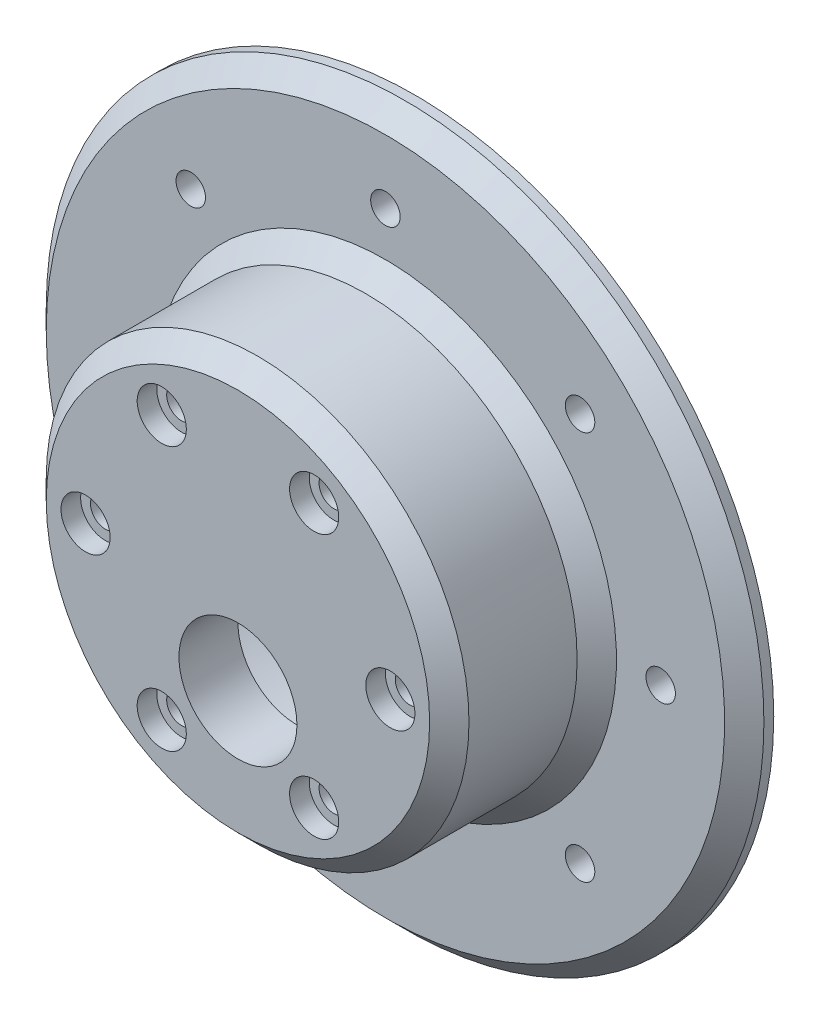
SolidWorks part; units mm, degrees
material "2014 Alloy"
ref_plane "Front Plane" through (0, 0, 0) normal (0, 0, 1) x (1, 0, 0)
ref_plane "Top Plane" through (0, 0, 0) normal (0, 1, 0) x (1, 0, 0)
ref_plane "Right Plane" through (0, 0, 0) normal (1, 0, 0) x (0, 0, -1)
sketch "Sketch1" plane through (0, 0, 0) normal (1, 0, 0) x (0, 0, -1)
  line L0 (0, 0) -> (0, 18.5)
  line L1 (0, 18.5) -> (12, 18.5)
  line L2 (12, 18.5) -> (12, 23.5)
  line L3 (9, 21.5) -> (-6, 21.5)
  line L4 (-6, 21.5) -> (-6, 0)
  line L5 (-6, 0) -> (0, 0)
  line L6 (12, 23.5) -> (11, 23.5)
  line L7 (11, 23.5) -> (11, 25.5)
  line L8 (12, 36.5) -> (9, 36.5)
  line L9 (9, 36.5) -> (9, 21.5)
  line L10 (11, 25.5) -> (12, 25.5)
  line L11 (12, 25.5) -> (12, 36.5)
  dimension "D1" = 18.5
  dimension "D2" = 6
  dimension "D3" = 3
  dimension "D4" = 15
  dimension "D5" = 3
  dimension "D6" = 15
  dimension "D7" = 5
  dimension "D8" = 1
  dimension "D9" = 2
revolve "Revolve1" add sketch "Sketch1" angle 360 about L5
sketch "Sketch2" plane through (0, 0, 6) normal (0, 0, 1) x (1, 0, 0)
  line L0 (0, 0) -> (21.5, 0) construction
  circle A0 centre (0, 0) radius 21.5 construction
hole_wizard "CBORE for M1.6 Hex Head Cap Screw1" positions "Sketch4" profile "Sketch3" counterbore size "M1.6" standard "ISO" end condition through all
sketch "Sketch4" plane through (0, 0, 6) normal (0, 0, 1) x (1, 0, 0)
  point P0 (15.5, 0)
  dimension "D1" = 15.5
sketch "Sketch3" plane through (15.5, 0, 6) normal (1, 0, 0) x (0, -1, 0)
  line L0 (0, 0) -> (0, 18)
  line L1 (0, 18) -> (1.5, 18)
  line L3 (1.5, 18) -> (1.5, 2)
  line L4 (1.5, 2) -> (2.5, 2)
  line L5 (2.5, 2) -> (2.5, 0)
  line L7 (2.5, 0) -> (0, 0)
  line L11 (0, -6.35) -> (0, 107.95) construction
  dimension "Thru Hole Dia." = 3
  dimension "Thru Hole Depth" = 18
  dimension "C'Bore Dia." = 5
  dimension "C'Bore Depth" = 2
pattern_circular "CirPattern1" count 6 over 360 about axis through (0, 0, 0) along (0, 0, 1) of "CBORE for M1.6 Hex Head Cap Screw1"
hole_wizard "Ø12.0mm Dowel Hole1" positions "Sketch6" profile "Sketch5" hole size "Ø12.0" standard "ISO"
sketch "Sketch6" plane through (0, 0, 6) normal (0, 0, 1) x (1, 0, 0)
  point P0 (0, -7)
  dimension "D1" = 7
sketch "Sketch5" plane through (0, -7, 6) normal (1, 0, 0) x (0, -1, 0)
  line L0 (0, 0) -> (0, 18.6052)
  line L1 (0, 18.6052) -> (6, 15)
  line L2 (6, 15) -> (6, 0)
  line L5 (6, 0) -> (0, 0)
  line L10 (0, 18.6052) -> (-6, 15) construction
  line L11 (0, -6.35) -> (0, 107.95) construction
  dimension "Hole Dia." = 12
  dimension "Hole Depth" = 15
  dimension "Drill Angle" = 118
chamfer "Chamfer1" distance 2 angle 45 3 edges at (21.5, 0, 6) (36.5, 0, -9) (21.5, 0, -9)
hole_wizard "Ø3.0mm Dowel Hole3" positions "Sketch8" profile "Sketch7" hole size "Ø3.0" standard "ISO"
sketch "Sketch8" plane through (0, 0, -9) normal (0, 0, 1) x (1, 0, 0)
  circle A0 centre (0, 0) radius 21.5 construction
  point P0 (0, 28)
  dimension "D1" = 28
sketch "Sketch7" plane through (0, 28, -9) normal (1, 0, 0) x (0, -1, 0)
  line L0 (0, 0) -> (0, 15.9013)
  line L1 (0, 15.9013) -> (1.5, 15)
  line L2 (1.5, 15) -> (1.5, 0)
  line L5 (1.5, 0) -> (0, 0)
  line L10 (0, 15.9013) -> (-1.5, 15) construction
  line L11 (0, -6.35) -> (0, 107.95) construction
  dimension "Hole Dia." = 3
  dimension "Hole Depth" = 15
  dimension "Drill Angle" = 118
pattern_circular "CirPattern2" count 8 over 360 about axis through (0, 0, 0) along (0, 0, 1) of "Ø3.0mm Dowel Hole3"
sketch "Sketch9" plane through (0, 0, -9) normal (0, 0, 1) x (1, 0, 0)
  circle A0 centre (0, 0) radius 28 construction
